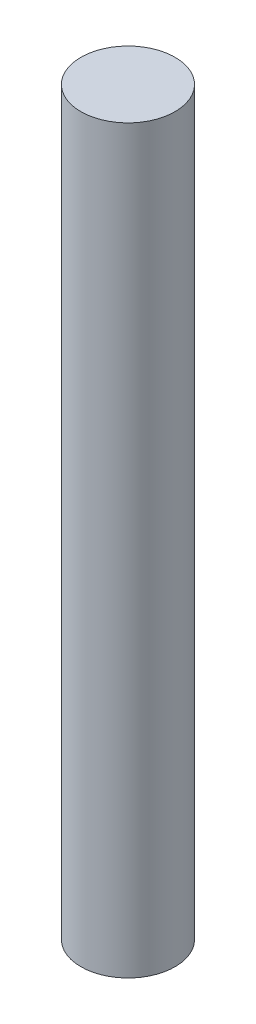
SolidWorks part; units mm, degrees
ref_plane "Front Plane" through (0, 0, 0) normal (0, 0, 1) x (1, 0, 0)
ref_plane "Top Plane" through (0, 0, 0) normal (0, 1, 0) x (1, 0, 0)
ref_plane "Right Plane" through (0, 0, 0) normal (1, 0, 0) x (0, 0, -1)
sketch "Sketch1" plane through (0, 0, 0) normal (0, 1, 0) x (1, 0, 0)
  circle A0 centre (0, 0) radius 15.9
extrude "Boss-Extrude1" add sketch "Sketch1" along normal blind 250
